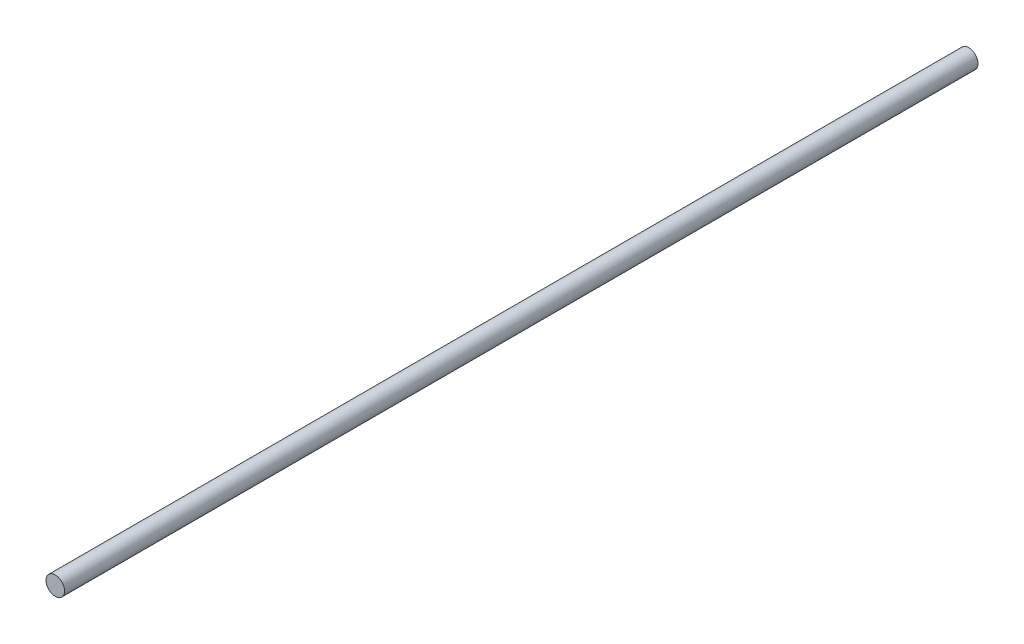
SolidWorks part; units mm, degrees
ref_plane "Front Plane" through (0, 0, 0) normal (0, 0, 1) x (1, 0, 0)
ref_plane "Top Plane" through (0, 0, 0) normal (0, 1, 0) x (1, 0, 0)
ref_plane "Right Plane" through (0, 0, 0) normal (1, 0, 0) x (0, 0, -1)
sketch "Sketch1" plane through (0, 0, 0) normal (0, 0, 1) x (1, 0, 0)
  circle A0 centre (0, 0) radius 3
  dimension "D1" = 6
extrude "Boss-Extrude1" add sketch "Sketch1" along normal blind 295
